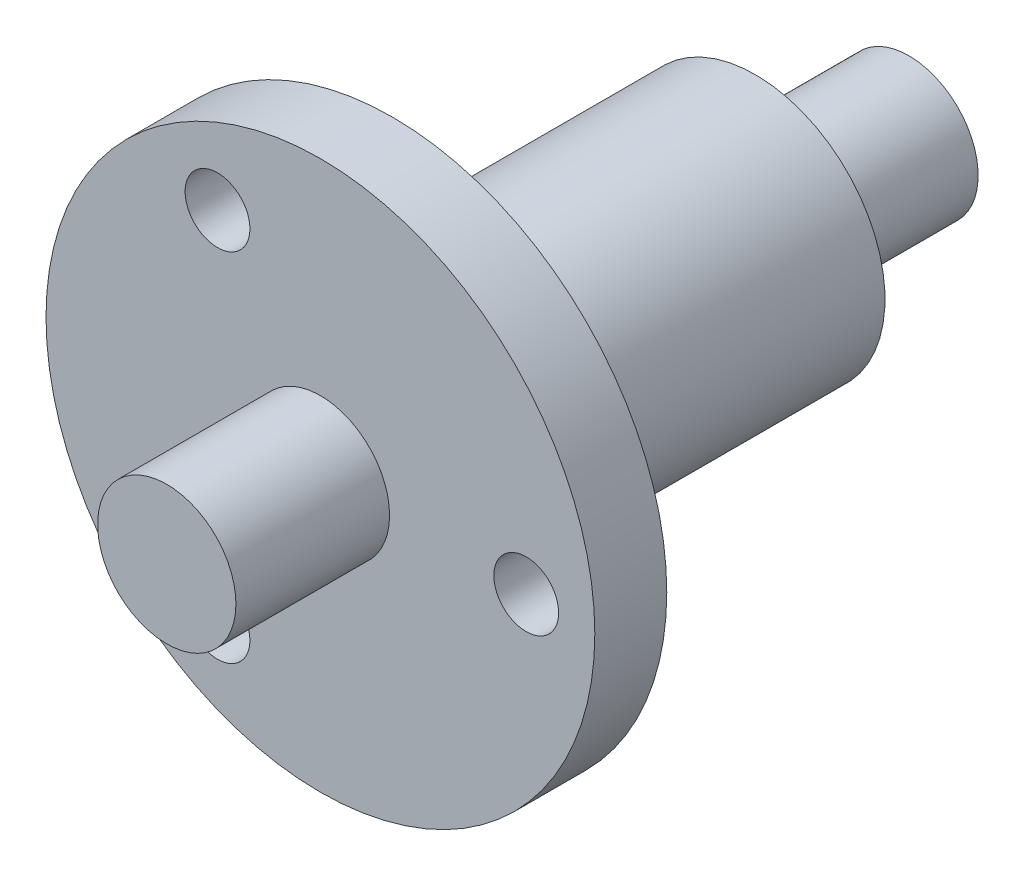
SolidWorks part; units mm, degrees
ref_plane "Front Plane" through (0, 0, 0) normal (0, 0, 1) x (1, 0, 0)
ref_plane "Top Plane" through (0, 0, 0) normal (0, 1, 0) x (1, 0, 0)
ref_plane "Right Plane" through (0, 0, 0) normal (1, 0, 0) x (0, 0, -1)
sketch "Sketch1" plane through (0, 0, 0) normal (0, 0, 1) x (1, 0, 0)
  circle A0 centre (0, 0) radius 12.7
extrude "Boss-Extrude1" add sketch "Sketch1" along normal blind 3.33
sketch "Sketch2" plane through (0, 0, 3.33) normal (0, 0, 1) x (1, 0, 0)
  circle A0 centre (0, 0) radius 3.2
extrude "Boss-Extrude2" add sketch "Sketch2" along normal blind 7.11
sketch "Sketch3" plane through (0, 0, 0) normal (0, 0, -1) x (-1, 0, 0)
  circle A0 centre (0, 0) radius 6
extrude "Boss-Extrude3" add sketch "Sketch3" along normal blind 16.8
sketch "Sketch4" plane through (0, 0, -16.8) normal (0, 0, -1) x (-1, 0, 0)
  circle A0 centre (0, 0) radius 3.2
extrude "Boss-Extrude4" add sketch "Sketch4" along normal blind 7.11
sketch "Sketch5" plane through (0, 0, 3.33) normal (0, 0, 1) x (1, 0, 0)
  circle A1 centre (9.525, 0) radius 1.5
  circle A2 centre (-4.7625, -8.2489) radius 1.5
  circle A3 centre (-4.7625, 8.2489) radius 1.5
  point P10 (0, 0)
  dimension "D1" = 3
extrude "Cut-Extrude1" cut sketch "Sketch5" against normal blind 7.11
